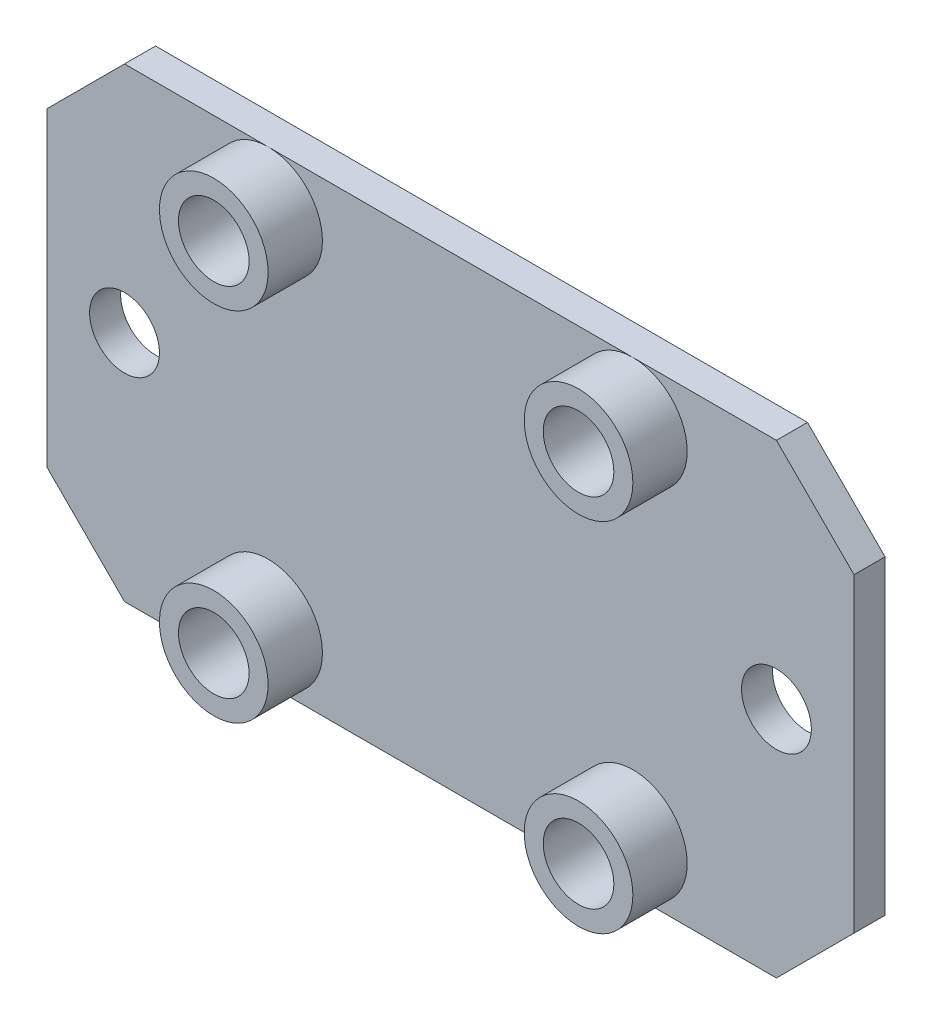
SolidWorks part; units mm, degrees
material "ABS"
ref_plane "正面" through (0, 0, 0) normal (1, 0, 0) x (0, 1, 0)
ref_plane "平面" through (0, 0, 0) normal (0, 0, 1) x (0, 1, 0)
ref_plane "右側面" through (0, 0, 0) normal (0, 1, 0) x (-1, 0, 0)
sketch "ｽｹｯﾁ1" plane through (0, 0, 0) normal (0, 0, 1) x (0, 1, 0)
  line L1 (0, 0) -> (30, 0)
  line L2 (0, 0) -> (0, 52)
  line L3 (0, 52) -> (30, 52)
  line L4 (30, 0) -> (30, 52)
  line L5 (0, 0) -> (30, 52) construction
  line L6 (0, 52) -> (30, 0) construction
  point P4 (15, 26)
  dimension "D1" = 30
  dimension "D2" = 52
extrude "ﾎﾞｽ - 押し出し1" add sketch "ｽｹｯﾁ1" along normal blind 2
sketch "ｽｹｯﾁ2" plane through (0, 0, 2) normal (0, 0, 1) x (1, 0, 0)
  line L0 (-37.75, 26.5) -> (-37.75, 3.5) construction
  line L1 (-37.75, 3.5) -> (-14.25, 3.5) construction
  line L2 (-14.25, 3.5) -> (-14.25, 26.5) construction
  line L3 (-14.25, 26.5) -> (-37.75, 26.5) construction
  line L4 (-52, 30) -> (-52, 0) construction
  line L5 (0, 30) -> (-52, 30) construction
  circle A0 centre (-37.75, 26.5) radius 3.5
  circle A1 centre (-14.25, 26.5) radius 3.5
  circle A2 centre (-14.25, 3.5) radius 3.5
  circle A3 centre (-37.75, 3.5) radius 3.5
  point P10 (-52, 15)
  point P11 (-37.75, 15)
  point P14 (-26, 30)
  point P15 (-26, 26.5)
  dimension "D1" = 7
  dimension "D2" = 23.5
  dimension "D3" = 23
extrude "ﾎﾞｽ - 押し出し2" add sketch "ｽｹｯﾁ2" along normal blind 3.5
sketch "ｽｹｯﾁ5" plane through (0, 0, 5.5) normal (0, 0, 1) x (1, 0, 0)
  circle A0 centre (-37.75, 26.5) radius 2.275
  circle A1 centre (-14.25, 26.5) radius 2.275
  circle A2 centre (-14.25, 3.5) radius 2.275
  circle A3 centre (-37.75, 3.5) radius 2.275
  dimension "D1" = 4.55
extrude "ｶｯﾄ - 押し出し1" cut sketch "ｽｹｯﾁ5" against normal blind 3.5
sketch "ｽｹｯﾁ3" plane through (0, 0, 2) normal (0, 0, 1) x (1, 0, 0)
  line L0 (-52, 30) -> (-52, 0) construction
  line L1 (0, 0) -> (0, 30) construction
  point P0 (-47, 15)
  point P1 (-5, 15)
  point P4 (-52, 15)
  dimension "D1" = 5
  dimension "D2" = 5
hole_wizard "M4 すきま穴1" positions "ｽｹｯﾁ3" profile "ｽｹｯﾁ4" hole size "M4" standard "JIS" end condition through all
sketch "ｽｹｯﾁ4" plane through (-47, 15, 2) normal (1, 0, 0) x (0, -1, 0)
  line L0 (0, 0) -> (0, 2)
  line L1 (0, 2) -> (2.25, 2)
  line L2 (2.25, 2) -> (2.25, 0)
  line L5 (2.25, 0) -> (0, 0)
  line L11 (0, -6.35) -> (0, 107.95) construction
  dimension "通し穴の直径" = 4.5
  dimension "通し穴の深さ" = 2
chamfer "面取り1" distance 5 angle 45 4 edges at (-52, 0, 1) (0, 0, 1) (0, 30, 1) (-52, 30, 1)
